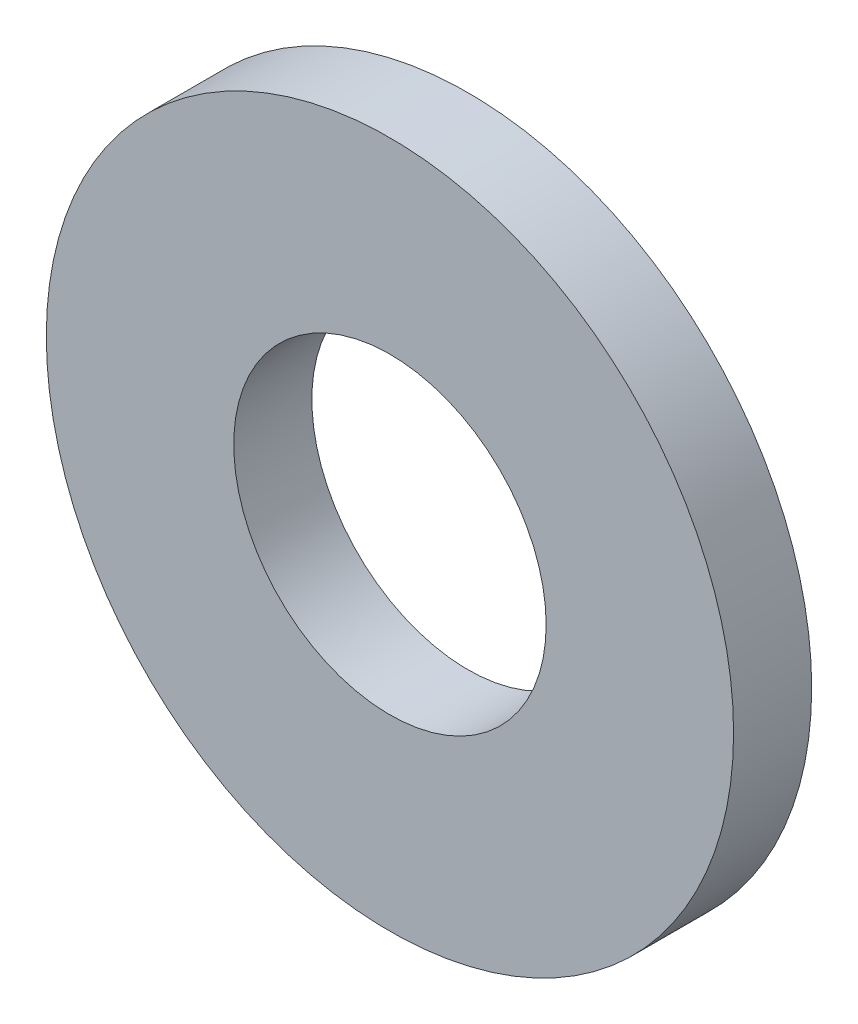
SolidWorks part; units mm, degrees
ref_plane "Front Plane" through (0, 0, 0) normal (0, 0, 1) x (1, 0, 0)
ref_plane "Top Plane" through (0, 0, 0) normal (0, 1, 0) x (1, 0, 0)
ref_plane "Right Plane" through (0, 0, 0) normal (1, 0, 0) x (0, 0, -1)
sketch "Sketch1" plane through (0, 0, 0) normal (0, 0, 1) x (1, 0, 0)
  circle A0 centre (0, 0) radius 2.54
  circle A1 centre (0, 0) radius 5.588
  point P4 (-2.54, 0)
  dimension "ID" = 5.08
  dimension "OD" = 11.176
extrude "Extrude1" add sketch "Sketch1" against normal blind 1.27
